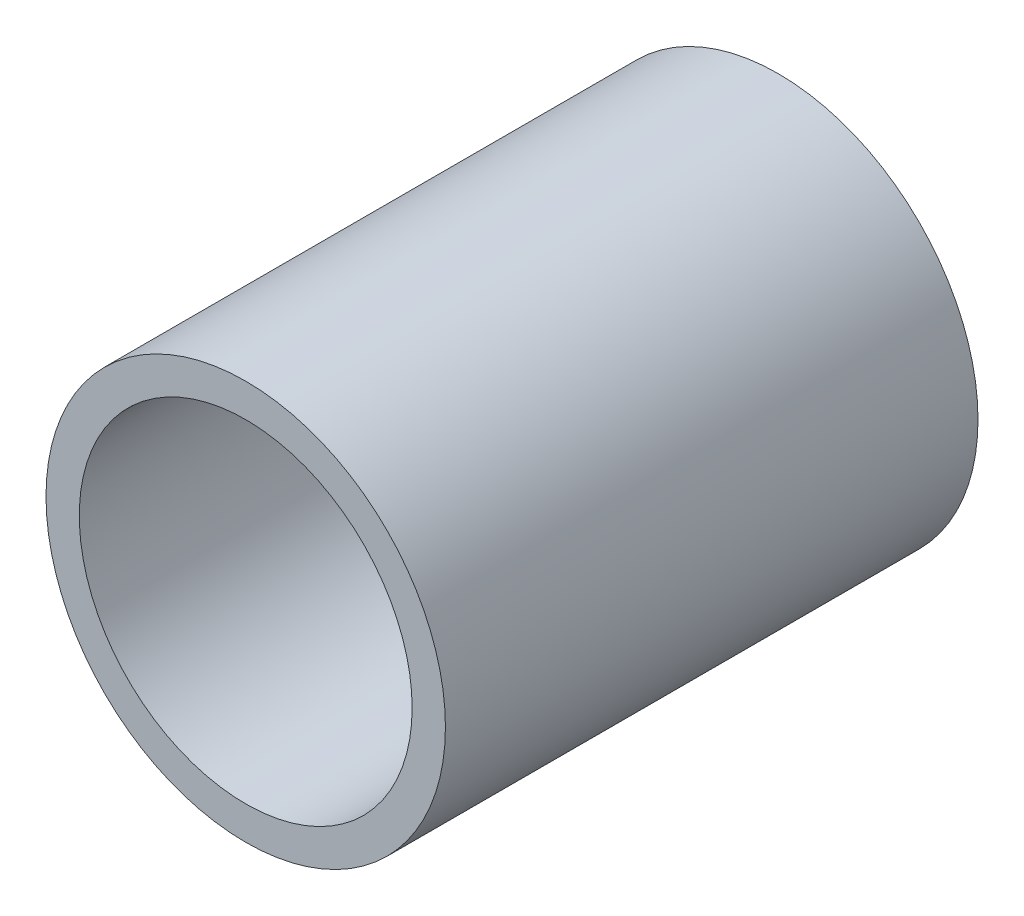
SolidWorks part; units mm, degrees
ref_plane "Front Plane" through (0, 0, 0) normal (0, 0, 1) x (1, 0, 0)
ref_plane "Top Plane" through (0, 0, 0) normal (0, 1, 0) x (1, 0, 0)
ref_plane "Right Plane" through (0, 0, 0) normal (1, 0, 0) x (0, 0, -1)
sketch "Sketch1" plane through (0, 0, 0) normal (0, 0, 1) x (1, 0, 0)
  circle A0 centre (0, 0) radius 3
  dimension "D1" = 6
extrude "Boss-Extrude1" add sketch "Sketch1" along normal blind 8
sketch "Sketch2" plane through (0, 0, 8) normal (0, 0, 1) x (1, 0, 0)
  circle A0 centre (0, 0) radius 2.5
  dimension "D1" = 5
extrude "Cut-Extrude1" cut sketch "Sketch2" against normal blind 7
